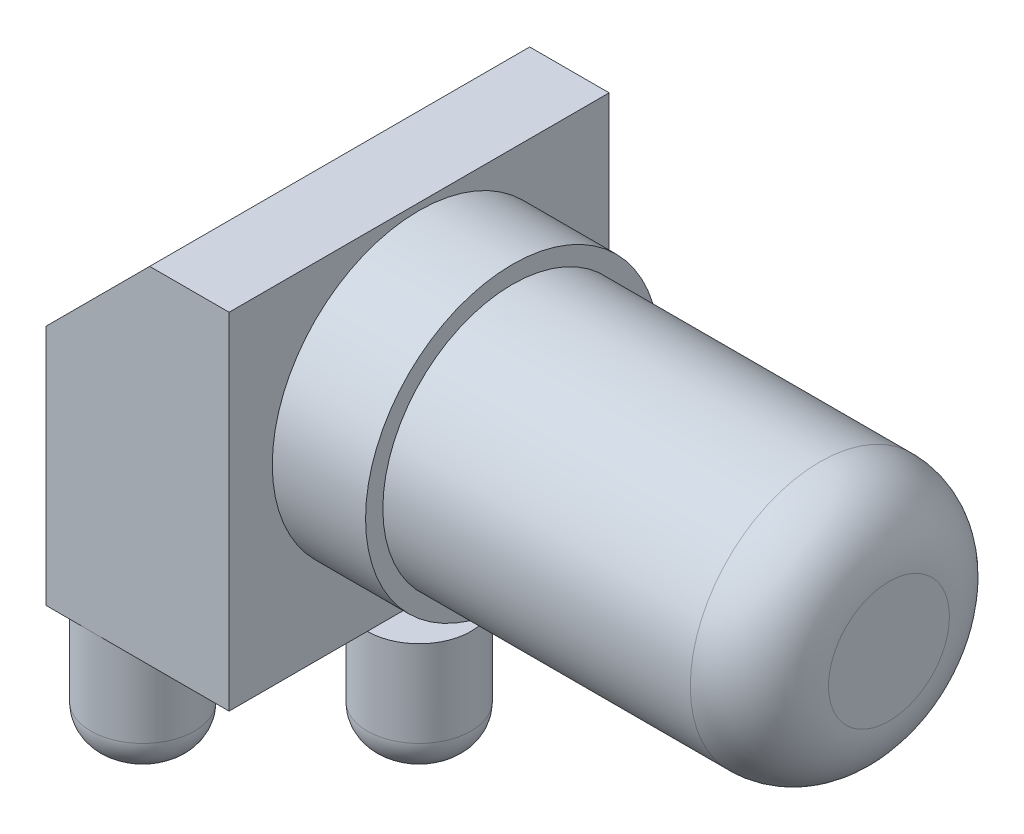
SolidWorks part; units mm, degrees
ref_plane "Front Plane" through (0, 0, 0) normal (0, 0, 1) x (1, 0, 0)
ref_plane "Top Plane" through (0, 0, 0) normal (0, 1, 0) x (1, 0, 0)
ref_plane "Right Plane" through (0, 0, 0) normal (1, 0, 0) x (0, 0, -1)
sketch "Sketch1" plane through (0, 0, 0) normal (0, 1, 0) x (1, 0, 0)
  circle A0 centre (0.635, 5.08) radius 1.905
  circle A1 centre (0.635, -5.08) radius 1.905
  circle A2 centre (5.715, 0) radius 1.905
  circle A3 centre (0, 0) radius 1.27
  point P0 (0, 0)
extrude "Boss-Extrude1" add sketch "Sketch1" against normal blind 4.445
sketch "Sketch2" plane through (0, 0, 0) normal (0, 1, 0) x (-1, 0, 0)
  line L0 (1.016, -6.985) -> (1.016, 6.985)
  line L1 (1.016, 6.985) -> (-5.715, 6.985)
  line L2 (1.016, -6.985) -> (-5.715, -6.985)
  line L4 (-5.715, -6.985) -> (-5.715, 6.985)
  circle A1 centre (-5.715, 0) radius 1.905 construction
  dimension "D1" = 13.97
  dimension "D2" = 6.731
  dimension "D3" = 6.985
extrude "Boss-Extrude2" add sketch "Sketch2" along normal blind 12.7
chamfer "Chamfer1" distance 3.81 angle 45 1 edges at (-1.016, 12.7, 0)
sketch "Sketch3" plane through (5.715, 0, 0) normal (1, 0, 0) x (0, 0, -1)
  circle A0 centre (0, 7.0485) radius 5.3975
  dimension "D1" = 7.0485
  dimension "D2" = 0
extrude "Boss-Extrude3" add sketch "Sketch3" along normal blind 3.429
sketch "Sketch4" plane through (9.144, 0, 0) normal (1, 0, 0) x (0, 0, -1)
  circle A0 centre (0, 7.0485) radius 4.7625
extrude "Boss-Extrude4" add sketch "Sketch4" along normal blind 13.843
fillet "Fillet1" radius 2.54 1 edges at (22.987, 7.0485, -4.7625)
fillet "Fillet2" radius 1.27 4 edges at (0, -4.445, 1.27) (0.635, -4.445, -3.175) (5.715, -4.445, 1.905) (0.635, -4.445, 6.985)
